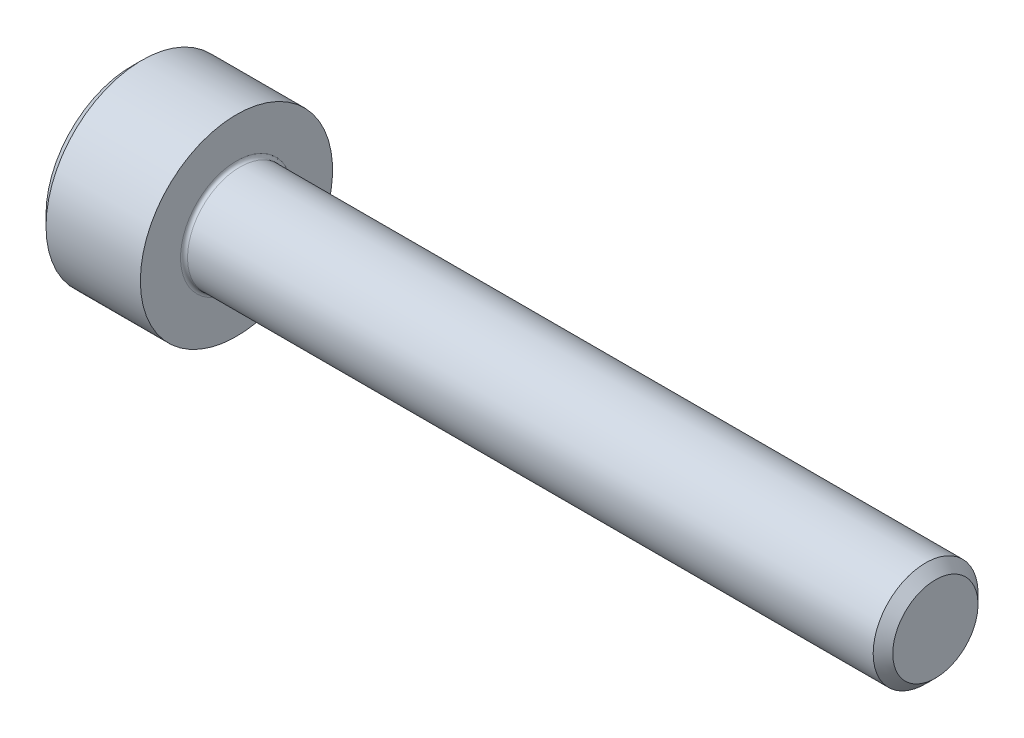
SolidWorks part; units mm, degrees
revolve "Base-Revolve" add sketch "BodySke"
sketch "BodySke" plane through (0, 0, 0) normal (0, 0, 1) x (1, 0, 0)
  line L0 (0, 0) -> (0, 2.45)
  line L1 (0.3, 2.75) -> (3, 2.75)
  line L2 (3, 2.75) -> (3, 1.5)
  line L3 (3, 1.5) -> (22.7195, 1.5)
  line L4 (23, 1.2195) -> (23, 0)
  line L5 (23, 0) -> (0, 0)
  line L6 (-31.75, 0) -> (127, 0) construction
  line L7 (0, 2.45) -> (0.3, 2.75)
  line L8 (23, 1.2195) -> (22.7195, 1.5)
  line L9 (0, -2.45) -> (0.3, -2.75) construction
  line L10 (23, -1.2195) -> (22.7195, -1.5) construction
  line L11 (3.5, 9.525) -> (3.5, 3.175) construction
  line L12 (3, 9.525) -> (3, 3.175) construction
  line L13 (-27, 9.525) -> (-27, 3.175) construction
  dimension "Diameter" = 3
  dimension "Head_ht" = 3
  dimension "Length" = 20
  dimension "Body_ch_ang" = 45
  dimension "Head_dia" = 5.5
  dimension "Head_ch_ang" = 45
  dimension "Minor_dia" = 2.439
  dimension "Advance" = 0.5
  dimension "Thread_nom" = 20
  dimension "Thread_length" = 50
  dimension "Head_ch_ht" = 0.3
cosmetic thread "ThreadCosmetic" [suppressed]
fillet "Fillet1" radius 0.1 1 edges at (3, 0, 1.5)
ref_plane "Plane1" through (0, 0, 0) normal (0, 0, 1) x (1, 0, 0)
ref_plane "Plane2" through (0, 0, 0) normal (0, 1, 0) x (1, 0, 0)
ref_plane "Plane3" through (0, 0, 0) normal (1, 0, 0) x (0, 0, -1)
other "Configuration Table"
sketch "Sketch2" plane through (0, 0, 0) normal (0, 0, 1) x (1, 0, 0)
  line L0 (0, 1.28) -> (1.3, 1.28)
  line L1 (1.3, 1.28) -> (2.039, 0)
  line L2 (-31.75, 0) -> (127, 0) construction
  line L3 (2.039, 0) -> (0, 0)
  line L4 (0, 0) -> (0, 1.28)
  line L5 (0, 2.45) -> (0, -2.45) construction
  line L6 (0, 0) -> (47.625, 0) construction
  line L7 (3, -2.75) -> (3, 2.75) construction
  dimension "D1" = 1.28
  dimension "D2" = 60
revolve "Hex-PreBroach" cut sketch "Sketch2" angle 360 about L6
sketch "Sketch3" plane through (0, 0, 0) normal (-1, 0, 0) x (0, 0.5, 0.866)
  line L0 (0.739, 1.28) -> (-0.739, 1.28)
  line L1 (-0.739, 1.28) -> (-1.478, 0)
  line L2 (0.739, 1.28) -> (1.478, 0)
  line L3 (0.739, -1.28) -> (1.478, 0)
  line L4 (0.739, -1.28) -> (-0.739, -1.28)
  line L5 (-0.739, -1.28) -> (-1.478, 0)
  dimension "D1" = 1.28
  dimension "D2" = 1.28
  dimension "Hex_size" = 2.56
extrude "Hex" cut sketch "Sketch3" against normal blind 1.3
sketch "Sketch4" plane through (0, 0, 0) normal (-1, 0, 0) x (0, 0, 1)
  line L0 (0, 0) -> (1.4605, 0)
  line L1 (0, 0) -> (6.1484, 3.5498) construction
  line L2 (0, 0) -> (0.7302, 1.2648)
  line L3 (1.2009, 0.3267) -> (1.3933, 0.4378)
  line L4 (0.8834, 0.8767) -> (1.0758, 0.9877)
  arc A0 (1.2009, 0.3267) -> (0.8834, 0.8767) centre (0, 0) ccw
  arc A1 (1.4605, 0) -> (1.3933, 0.4378) centre (0, 0) ccw
  arc A2 (0.7302, 1.2648) -> (1.0758, 0.9877) centre (0, 0) cw
  dimension "D1" = 30
  dimension "D2" = 60
  dimension "Spline_p_dim" = 0.635
  dimension "D3" = 0.3175
extrude "Spline" [suppressed] cut sketch "Sketch4" against normal blind 1.3
pattern_circular "CirPattern1" [suppressed] count 6 every 60
sketch "Sketch5" plane through (0, 0, 0) normal (0, 0, 1) x (1, 0, 0)
  line L0 (-31.75, 0) -> (127, 0) construction
  line L2 (0, 2.45) -> (0, -2.45) construction
  circle A0 centre (1.2, 0) radius 0.475
  dimension "Drilled_hole_dia" = 0.95
  dimension "Drilled_hole_loc" = 1.2
extrude "Hole" [suppressed] cut sketch "Sketch5" against normal through all and the other way through all
pattern_circular "Drilled-4" [suppressed] count 2 every 60
pattern_circular "Drilled-6" [suppressed] count 3 every 60
sketch "ThdSchSke" plane through (0, 0, 0) normal (0, 0, 1) x (1, 0, 0)
  line L0 (3.5, -1.2195) -> (3.3036, -1.5)
  line L1 (3.5, -1.2195) -> (3.6964, -1.5)
  line L2 (3.6964, -1.5) -> (3.6964, -1.875)
  line L3 (-3.175, 0) -> (5.1513, 0) construction
  line L5 (3.6964, -1.875) -> (3.3036, -1.875)
  line L6 (3.3036, -1.875) -> (3.3036, -1.5)
  line L7 (0, 2.45) -> (0, -2.45) construction
  dimension "Thread_minor" = 2.439
  dimension "Diameter" = 3
  dimension "Start" = 3.5
revolve "ThreadSchematic" [suppressed] cut sketch "ThdSchSke" angle 360 about L3
pattern_linear "ThdSchPat" [suppressed]
equation "\"D2@Sketch3\" = \"Hex_size@Sketch3\" / 2"
equation "\"D1@Sketch3\" = \"Hex_size@Sketch3\" / 2"
equation "\"D1@Sketch2\" = \"Hex_size@Sketch3\" / 2"
equation "\"D3@Sketch4\" = \"Spline_p_dim@Sketch4\" / 2"
equation "\"Thread_minor@ThreadCosmetic\"  =  \"Minor_dia@BodySke\""
equation "\"D2@CirPattern1\" = 360 / \"Num_teeth@CirPattern1\""
equation "\"Wall_thickness@Sketch2\" = \"Head_ht@BodySke\" - \"Key_eng@Hex\""
equation "\"Thread_length@ThreadCosmetic\" = ((sgn( (\"Length@BodySke\" - \"Advance@BodySke\" ) - \"Thread_nom@BodySke\" )-1)*( (\"Length@BodySke\" - \"Advance@BodySke\" ) - \"Thread_nom@BodySke\" ))/-2+ \"Thread_nom@BodySke\""
equation "\"Thread_minor@ThdSchSke\" = \"Minor_dia@BodySke\""
equation "\"Diameter@ThdSchSke\" = \"Diameter@BodySke\""
equation "\"Overcut@ThdSchSke\" = \"Diameter@BodySke\" * 1.25"
equation "\"Start@ThdSchSke\" = \"Head_ht@BodySke\" + \"Length@BodySke\" - \"Thread_length@ThreadCosmetic\"  '---Non-countersunk---"
equation "\"Num_threads@ThdSchPat\" = int( \"Thread_length@ThreadCosmetic\" / \"Advance@BodySke\" + 0.999 )  + 1"
equation "\"Advance@ThdSchPat\" = \"Thread_length@ThreadCosmetic\" /  (\"Num_threads@ThdSchPat\" - 1) 'relax it"
equation "\"Num_threads@ThdSchPat\" = \"Num_threads@ThdSchPat\" - sgn( \"Num_threads@ThdSchPat\" - 1) '---chamfered tips only---"
